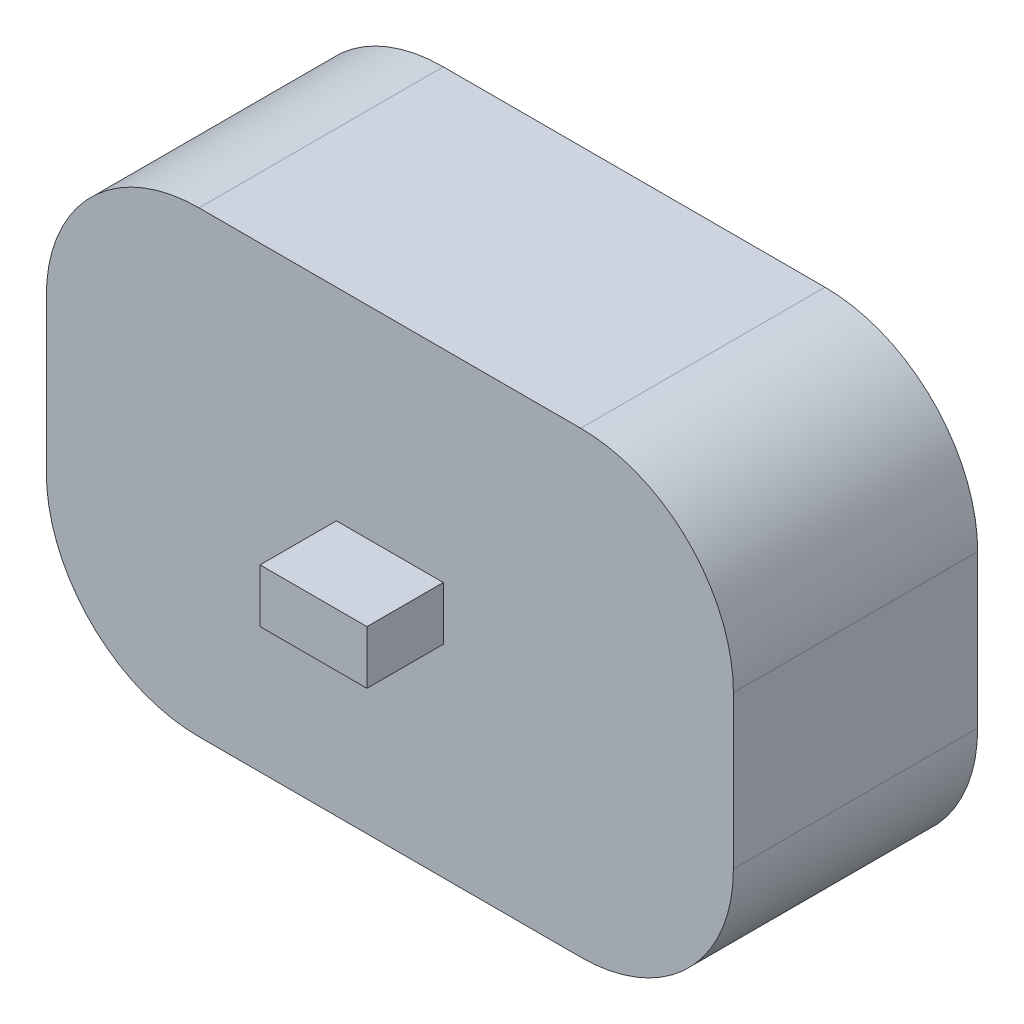
SolidWorks part; units mm, degrees
ref_plane "Front Plane" through (0, 0, 0) normal (0, 0, 1) x (1, 0, 0)
ref_plane "Top Plane" through (0, 0, 0) normal (0, 1, 0) x (1, 0, 0)
ref_plane "Right Plane" through (0, 0, 0) normal (1, 0, 0) x (0, 0, -1)
sketch "Sketch1" plane through (0, 0, 0) normal (0, 0, 1) x (1, 0, 0)
  line L1 (-22.5, -15) -> (22.5, -15)
  line L2 (-22.5, -15) -> (-22.5, 15)
  line L3 (-22.5, 15) -> (22.5, 15)
  line L4 (22.5, -15) -> (22.5, 15)
  line L5 (-22.5, -15) -> (22.5, 15) construction
  line L6 (-22.5, 15) -> (22.5, -15) construction
  point P0 (0, 0)
extrude "Boss-Extrude1" add sketch "Sketch1" along normal blind 16
sketch "Sketch2" plane through (0, 0, 16) normal (0, 0, 1) x (1, 0, 0)
  line L1 (3.5, 1.75) -> (-3.5, 1.75)
  line L2 (3.5, 1.75) -> (3.5, -1.75)
  line L3 (3.5, -1.75) -> (-3.5, -1.75)
  line L4 (-3.5, 1.75) -> (-3.5, -1.75)
  line L5 (3.5, 1.75) -> (-3.5, -1.75) construction
  line L6 (3.5, -1.75) -> (-3.5, 1.75) construction
  line L7 (-22.5, 15) -> (-22.5, -15) construction
  line L8 (22.5, 15) -> (-22.5, 15) construction
  point P0 (0, 0)
  point P5 (0, 0)
  point P7 (0, 0)
  point P9 (-22.5, 0)
  point P12 (0, 15)
  dimension "D1" = 7
  dimension "D2" = 3.5
  dimension "D3" = 19
  dimension "D4" = 13.25
extrude "Boss-Extrude2" add sketch "Sketch2" along normal blind 5 contours L3 L4 L1 L2
fillet "Fillet1" radius 10 4 edges at (-22.5, 15, 8) (22.5, 15, 8) (22.5, -15, 8) (-22.5, -15, 8)
